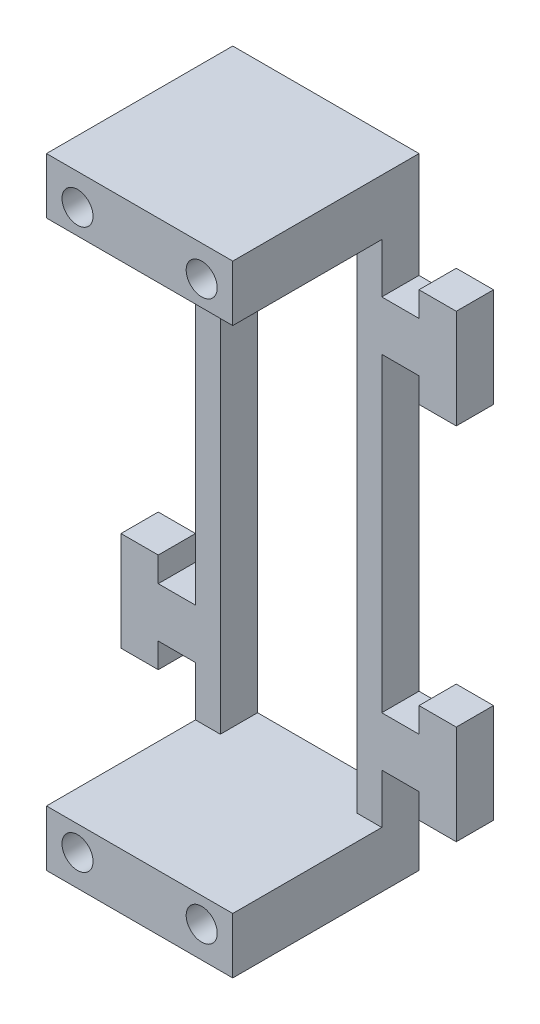
SolidWorks part; units mm, degrees
ref_plane "정면" through (0, 0, 0) normal (0, 0, 1) x (1, 0, 0)
ref_plane "윗면" through (0, 0, 0) normal (0, 1, 0) x (1, 0, 0)
ref_plane "우측면" through (0, 0, 0) normal (1, 0, 0) x (0, 0, -1)
sketch "스케치1" plane through (0, 0, 0) normal (0, 0, 1) x (1, 0, 0)
  line L0 (0, 0) -> (-13.1641, 0) construction
  line L1 (-7.5, 25) -> (7.5, 25)
  line L2 (-7.5, 25) -> (-7.5, -25)
  line L3 (-7.5, -25) -> (7.5, -25)
  line L4 (7.5, 25) -> (7.5, -25)
  line L5 (-7.5, 25) -> (7.5, -25) construction
  line L6 (-7.5, -25) -> (7.5, 25) construction
  point P0 (0, 0)
  dimension "D1" = 15
  dimension "D2" = 50
extrude "보스-돌출1" add sketch "스케치1" along normal blind 3
sketch "스케치2" plane through (0, 0, 0) normal (0, 0, -1) x (-1, 0, 0)
  line L0 (7.5, 25) -> (7.5, -25) construction
  line L1 (-7.5, 25) -> (7.5, 25)
  line L2 (-7.5, 25) -> (-7.5, 20.5)
  line L3 (-7.5, 20.5) -> (7.5, 20.5)
  line L4 (7.5, 25) -> (7.5, 20.5)
  line L5 (-7.5, 25) -> (7.5, 20.5) construction
  line L6 (-7.5, 20.5) -> (7.5, 25) construction
  line L7 (-7.5, 25) -> (7.5, 25) construction
  line L9 (0, 0) -> (13.4402, 0) construction
  line L10 (-7.5, -20.5) -> (7.5, -25) construction
  line L11 (-7.5, -25) -> (7.5, -20.5) construction
  line L12 (7.5, -25) -> (7.5, -20.5)
  line L13 (-7.5, -20.5) -> (7.5, -20.5)
  line L14 (-7.5, -25) -> (-7.5, -20.5)
  line L15 (-7.5, -25) -> (7.5, -25)
  line L23 (0, 0) -> (0, 6.6313) construction
  point P0 (0, 22.75)
  point P19 (0, -22.75)
  dimension "D1" = 4.5
extrude "보스-돌출2" add sketch "스케치2" along normal blind 12
sketch "스케치3" plane through (0, 0, -12) normal (0, 0, -1) x (-1, 0, 0)
  line L0 (0, 0) -> (0, 9.7101) construction
  line L1 (-7.5, 25) -> (7.5, 25)
  line L2 (-7.5, 25) -> (-7.5, -25)
  line L3 (-7.5, -25) -> (7.5, -25)
  line L4 (7.5, 25) -> (7.5, -25)
  line L5 (-7.5, 25) -> (7.5, -25) construction
  line L6 (-7.5, -25) -> (7.5, 25) construction
  line L7 (-5.5, 20.5) -> (5.5, 20.5)
  line L8 (-5.5, 20.5) -> (-5.5, -20.5)
  line L17 (5.5, -20.5) -> (-5.5, -20.5)
  line L18 (5.5, 20.5) -> (5.5, -20.5)
  line L21 (0, 0) -> (18.5385, 0) construction
  point P0 (0, 0)
  point P7 (0, 0)
  point P9 (-6, -20)
  point P12 (4.4222, 20)
  dimension "D1" = 41
  dimension "D2" = 11
  dimension "D3" = 20.5
extrude "보스-돌출3" add sketch "스케치3" along normal blind 3
sketch "스케치5" plane through (0, 0, -15) normal (0, 0, -1) x (-1, 0, 0)
  line L0 (-7.5, 16.5) -> (-10.5, 16.5)
  line L2 (-10.5, 16.5) -> (-10.5, 18.5)
  line L3 (-10.5, 18.5) -> (-13.5, 18.5)
  line L4 (-13.5, 18.5) -> (-13.5, 10.5)
  line L5 (-13.5, 10.5) -> (-10.5, 10.5)
  line L6 (-10.5, 10.5) -> (-10.5, 12.5)
  line L7 (-10.5, 12.5) -> (-7.5, 12.5)
  line L8 (-7.5, 16.5) -> (-7.5, 12.5)
  line L9 (-7.5, 14.5) -> (-13.1442, 14.5) construction
  line L11 (0, 0) -> (0, 7.6378) construction
  line L12 (0, 0) -> (17.2492, 0) construction
  line L13 (7.5, 14.5) -> (13.1442, 14.5) construction
  line L14 (7.5, 16.5) -> (7.5, 12.5)
  line L15 (10.5, 12.5) -> (7.5, 12.5)
  line L16 (10.5, 10.5) -> (10.5, 12.5)
  line L17 (13.5, 10.5) -> (10.5, 10.5)
  line L18 (13.5, 18.5) -> (13.5, 10.5)
  line L19 (10.5, 18.5) -> (13.5, 18.5)
  line L20 (10.5, 16.5) -> (10.5, 18.5)
  line L21 (7.5, 16.5) -> (10.5, 16.5)
  line L22 (7.5, -14.5) -> (13.1442, -14.5) construction
  line L23 (-7.5, -14.5) -> (-13.1442, -14.5) construction
  line L24 (7.5, -16.5) -> (10.5, -16.5)
  line L25 (10.5, -16.5) -> (10.5, -18.5)
  line L26 (10.5, -18.5) -> (13.5, -18.5)
  line L27 (13.5, -18.5) -> (13.5, -10.5)
  line L28 (13.5, -10.5) -> (10.5, -10.5)
  line L29 (10.5, -10.5) -> (10.5, -12.5)
  line L30 (10.5, -12.5) -> (7.5, -12.5)
  line L31 (7.5, -16.5) -> (7.5, -12.5)
  line L32 (-7.5, -16.5) -> (-7.5, -12.5)
  line L33 (-10.5, -12.5) -> (-7.5, -12.5)
  line L34 (-10.5, -10.5) -> (-10.5, -12.5)
  line L35 (-13.5, -10.5) -> (-10.5, -10.5)
  line L36 (-13.5, -18.5) -> (-13.5, -10.5)
  line L37 (-10.5, -18.5) -> (-13.5, -18.5)
  line L38 (-10.5, -16.5) -> (-10.5, -18.5)
  line L39 (-7.5, -16.5) -> (-10.5, -16.5)
  line L40 (-7.5, -25) -> (-7.5, 25) construction
  dimension "D1" = 8
  dimension "D2" = 4
  dimension "D3" = 10.5
  dimension "D4" = 3
  dimension "D5" = 3
extrude "보스-돌출4" add sketch "스케치5" against normal blind 3
hole_wizard "M3 나사 구멍1" positions "스케치6" profile "스케치7" tap size "M3" standard "ISO" end condition up to next
sketch "스케치6" plane through (0, 0, 3) normal (0, 0, 1) x (1, 0, 0)
  line L0 (7.5, 25) -> (-7.5, 25) construction
  point P0 (0, 5)
  point P2 (0, -5)
  dimension "D1" = 10
  dimension "D2" = 20
sketch "스케치7" plane through (0, 5, 3) normal (1, 0, 0) x (0, -1, 0)
  line L0 (0, 0) -> (0, 3)
  line L1 (0, 3) -> (1.25, 3)
  line L2 (1.25, 3) -> (1.25, 0)
  line L5 (1.25, 0) -> (0, 0)
  line L11 (0, -6.35) -> (0, 107.95) construction
  dimension "관통 탭 드릴 지름" = 2.5
  dimension "관통 탭 드릴 깊이" = 3
cosmetic thread "구멍 나사산1" parameters "D2"=3
cosmetic thread "구멍 나사산2" parameters "D2"=3
sketch "스케치8" plane through (-7.5, 0, 0) normal (-1, 0, 0) x (0, 0, 1)
  line L0 (3, -25) -> (-15, -25) construction
  line L1 (3, 25) -> (0, 25)
  line L2 (3, 25) -> (3, -25)
  line L3 (3, -25) -> (0, -25)
  line L4 (0, 25) -> (0, -25)
  line L5 (0, 20.5) -> (0, -20.5) construction
extrude "컷-돌출1" cut sketch "스케치8" against normal up to next
hole_wizard "M3 나사 구멍2" positions "스케치9" profile "스케치10" tap size "M3" standard "ISO"
sketch "스케치9" plane through (0, 0, 0) normal (0, 0, 1) x (1, 0, 0)
  line L0 (-7.5, 25) -> (-7.5, 20.5) construction
  line L1 (7.5, 25) -> (-7.5, 25) construction
  line L2 (0, 0) -> (0, 12.2547) construction
  line L3 (0, -8.25) -> (0, 8.25) construction
  line L5 (0, 0) -> (18.5881, 0) construction
  point P0 (-5, 22.5)
  point P2 (5, 22.5)
  point P19 (0, 0)
  point P20 (-5, -22.5)
  point P21 (5, -22.5)
  dimension "D1" = 2.5
  dimension "D2" = 2.5
cosmetic thread "구멍 나사산3" parameters "D1"=15, "D2"=3
cosmetic thread "구멍 나사산4" parameters "D1"=15, "D2"=3
cosmetic thread "구멍 나사산5" parameters "D1"=15, "D2"=3
cosmetic thread "구멍 나사산6" parameters "D1"=15, "D2"=3
sketch "스케치10" plane through (-5, 22.5, 0) normal (1, 0, 0) x (0, -1, 0)
  line L0 (0, 0) -> (0, 10.7511)
  line L1 (0, 10.7511) -> (1.25, 10)
  line L2 (1.25, 10) -> (1.25, 0)
  line L5 (1.25, 0) -> (0, 0)
  line L10 (0, 10.7511) -> (-1.25, 10) construction
  line L11 (0, -6.35) -> (0, 107.95) construction
  dimension "탭 드릴 지름" = 2.5
  dimension "탭 드릴 깊이" = 10
  dimension "드릴 각도" = 118
